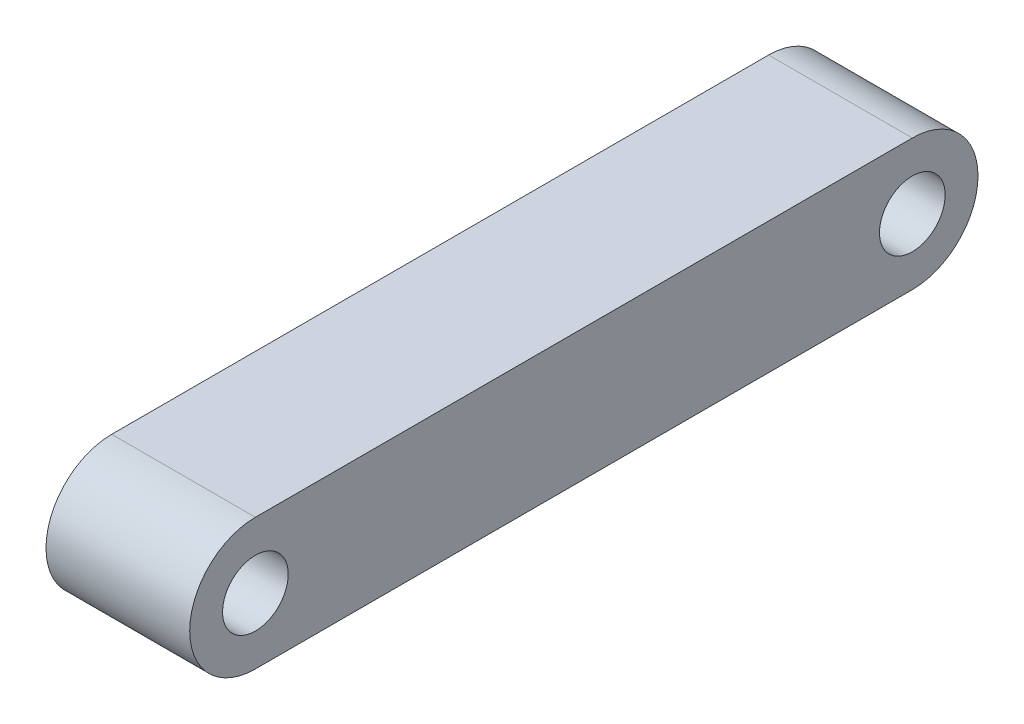
SolidWorks part; units mm, degrees
material "普通碳钢"
ref_plane "前视基准面" through (0, 0, 0) normal (0, 0, 1) x (1, 0, 0)
ref_plane "上视基准面" through (0, 0, 0) normal (0, 1, 0) x (1, 0, 0)
ref_plane "右视基准面" through (0, 0, 0) normal (1, 0, 0) x (0, 0, -1)
sketch "草图1" plane through (0, 0, 0) normal (1, 0, 0) x (0, 0, -1)
  line L0 (-40, 8) -> (40, 8)
  line L1 (-40, -8) -> (40, -8)
  line L2 (0, 0) -> (0, 27.9648) construction
  line L3 (40, 0) -> (0, 0) construction
  line L4 (0, 0) -> (-40, 0) construction
  circle A0 centre (40, 0) radius 4
  arc A1 (-40, -8) -> (-40, 8) centre (-40, 0) cw
  circle A2 centre (-40, 0) radius 4
  arc A3 (40, -8) -> (40, 8) centre (40, 0) ccw
  point P4 (0, 0)
  point P6 (0, -10)
  point P7 (0, 0)
  point P14 (0, 10)
  dimension "D1" = 8
  dimension "D2" = 8
  dimension "D4" = 8
  dimension "D3" = 40
  dimension "D5" = 40
extrude "凸台-拉伸1" add sketch "草图1" along normal blind 17.5
